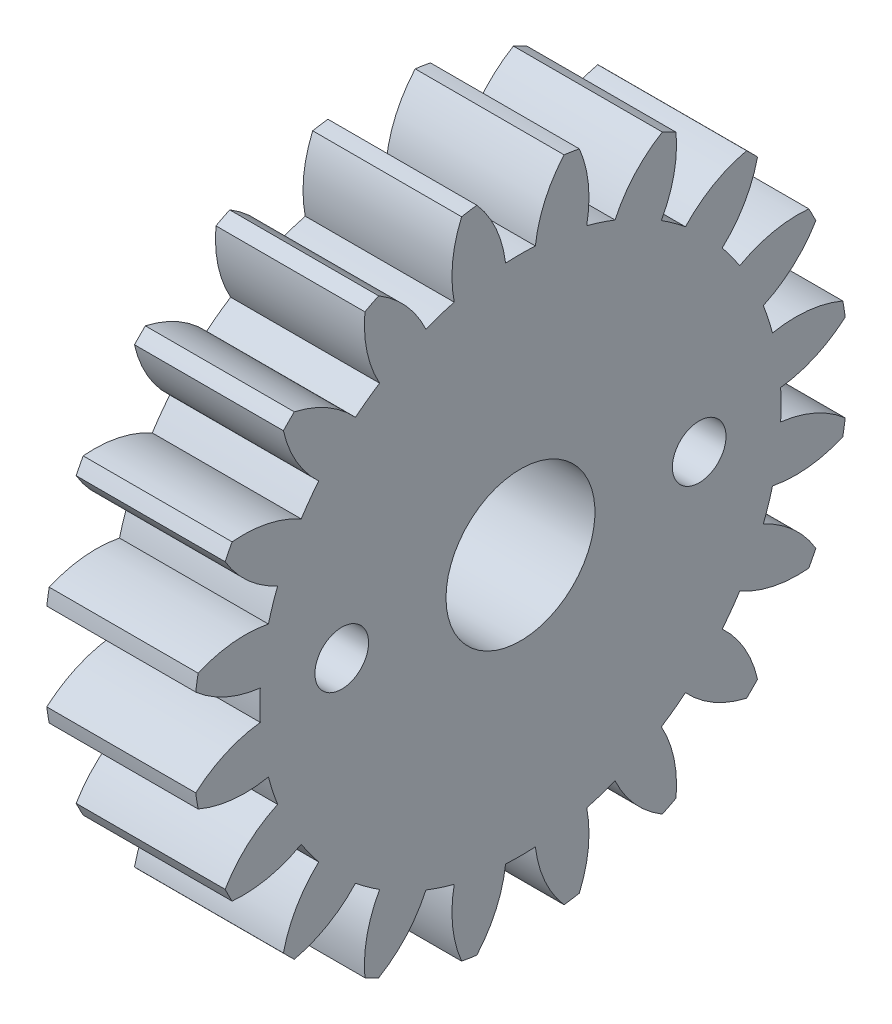
SolidWorks part; units mm, degrees
ref_plane "Plane1" through (0, 0, 0) normal (0, 0, 1) x (1, 0, 0)
ref_plane "Plane2" through (0, 0, 0) normal (0, 1, 0) x (1, 0, 0)
ref_plane "Plane3" through (0, 0, 0) normal (1, 0, 0) x (0, 0, -1)
sketch "HoldingSke" plane through (0, 0, 0) normal (0, 1, 0) x (1, 0, 0)
  line L0 (0, 0) -> (0.9397, -0.342)
  line L1 (-15, 0) -> (100, 0) construction
  line L2 (0, 0) -> (-2.1039, 2.3779)
  line L3 (0, 0) -> (-11.863, 4.5341)
  line L4 (0, 0) -> (8.1152, 2.9537)
  line L5 (0, 0) -> (-46.8476, -17.4728)
  line L6 (0, 0) -> (-4.1448, -2.7965)
  line L7 (-2.1039, 2.3779) -> (8.6586, 51.2059)
  line L8 (-76.2, 54.61) -> (-75.3, 54.61)
  line L9 (-71.009, 38.7566) -> (-53.1078, 45.2721)
  line L10 (-76.2, 71.12) -> (104.1128, 71.12)
  line L11 (0, 0) -> (-5, 0)
  line L12 (-76.2, 101.6) -> (-76.162, 101.6)
  line L13 (24.9733, 27.94) -> (52.9518, 28.4284)
  line L14 (24.9733, 27.94) -> (24.9743, 27.94)
  line L15 (24.9733, 27.94) -> (100.4006, 29.5858)
  line L16 (-63.627, -1) -> (-12.827, -1)
  circle A0 centre (0, 0) radius 2.5
  circle A1 centre (0, 0) radius 8.749
  circle A2 centre (0, 0) radius 37.5
  circle A3 centre (0, 0) radius 2.5
  dimension "MHD" = 17.498
  dimension "Hub_dia" = 75
  dimension "Bore" = 5
  dimension "MBD" = 5
  dimension "Num_teeth" = 20
  dimension "Pitch" = 1
  dimension "Overall_len" = 50
  dimension "Show_teeth" = 20
  dimension "Thickness" = 5
  dimension "OAL" = 50.0001
  dimension "T_dim" = 0.9
  dimension "Ap" = 20
  dimension "H" = 19.05
  dimension "Pitch_radius" = 180.3128
  dimension "Width" = 5
  dimension "Backlash" = 0.038
  dimension "Addendum_fac" = 1
  dimension "Dedendum_fac" = 1.25
  dimension "Clearance_fac" = 0.25
  dimension "Dedendum_add" = 0.001
  dimension "Module" = 1
sketch "BasProSke" plane through (0, 0, 0) normal (0, 1, 0) x (1, 0, 0)
  line L0 (-10, 0) -> (60, 0) construction
  line L1 (0, 0) -> (0, 11)
  line L2 (0, 0) -> (5, 0)
  line L3 (5, 0) -> (5, 11)
  line L4 (5, 11) -> (0, 11)
  dimension "Thickness" = 5
  dimension "Diameter" = 22
revolve "Base-Revolve" add sketch "BasProSke" angle 360 about L0
sketch "TooCutSke" plane through (0, 0, 0) normal (1, 0, 0) x (0, 0, -1)
  line L1 (0, 0) -> (0, 107) construction
  line L2 (0, 0) -> (-0.8511, 9.9637) construction
  line L3 (0, 0) -> (-3.1206, 19.7028) construction
  line L4 (-0.8511, 9.9637) -> (-1.5603, 9.8514) construction
  arc A0 (0.4999, 8.7347) -> (-0.4999, 8.7347) centre (0, 0) ccw
  arc A1 (1.4852, 10.9249) -> (-1.4852, 10.9249) centre (0, 0) ccw
  circle A2 centre (0, 0) radius 10 construction
  circle A3 centre (0, 0) radius 9.3969 construction
  arc A4 (-0.4999, 8.7347) -> (-1.4852, 10.9249) centre (-4.4722, 8.2645) ccw
  arc A5 (1.4852, 10.9249) -> (0.4999, 8.7347) centre (4.4722, 8.2645) ccw
  dimension "Root_dia" = 17.498
  dimension "Overcut_dia" = 22.0508
  dimension "Pitch_dia" = 20
  dimension "Base_dia" = 18.7939
  dimension "Flank_rad" = 4
  dimension "Half_ang" = 9
  dimension "Half_CT" = 0.7181
extrude "ToothCut" cut sketch "TooCutSke" along normal through all
fillet "Breaks" [suppressed] radius 0.02
fillet "RootFillets" [suppressed] radius 0.251
pattern_circular "TeethCuts" count 20 every 18 about axis through (-10, 0, 0) along (1, 0, 0) of "ToothCut", "RootFillets", "Breaks"
sketch "HubNeaOneSke" plane through (0, 0, 0) normal (-1, 0, 0) x (0, 0, 1)
  circle A0 centre (0, 0) radius 8.749
  dimension "Diameter" = 17.498
extrude "HubNearOne" [suppressed] add sketch "HubNeaOneSke" along normal blind 45.0001
sketch "HubNeaBotSke" plane through (0, 0, 0) normal (-1, 0, 0) x (0, 0, 1)
  circle A0 centre (0, 0) radius 8.749
  dimension "Diameter" = 17.498
extrude "HubNearBoth" [suppressed] add sketch "HubNeaBotSke" along normal blind 22.5
ref_plane "FarPln" through (5, 0, 0) normal (1, 0, 0) x (0, 0, -1)
sketch "HubFarSke" plane through (5, 0, 0) normal (1, 0, 0) x (0, 0, -1)
  circle A0 centre (0, 0) radius 8.749
  dimension "Diameter" = 17.498
extrude "HubFar" [suppressed] add sketch "HubFarSke" along normal blind 22.5
sketch "BorSke" plane through (0, 0, 0) normal (1, 0, 0) x (0, 0, -1)
  circle A0 centre (0, 0) radius 2.5
  dimension "Diameter" = 5
extrude "Bore" cut sketch "BorSke" along normal mid plane 100.0001
sketch "KeySke" plane through (0, 0, 0) normal (1, 0, 0) x (0, 0, -1)
  line L0 (-1, 0) -> (-1, 3.4)
  line L1 (-1, 3.4) -> (1, 3.4)
  line L2 (1, 3.4) -> (1, 0)
  line L3 (0, 0) -> (0, 34) construction
  line L4 (-1, 0) -> (1, 0)
  dimension "Offset" = 3.4
  dimension "Width" = 2
extrude "Keyway" [suppressed] cut sketch "KeySke" along normal mid plane 100.0001
pattern_circular "Keyway2" [suppressed] count 2 every 90 about axis through (-10, 0, 0) along (1, 0, 0)
sketch "Sketch1" plane through (5, 0, 0) normal (1, 0, 0) x (0, 0, -1)
  line L0 (0, 0) -> (6, 0) construction
  line L1 (0, 0) -> (0, 5.6094) construction
  circle A0 centre (6, 0) radius 0.9
  circle A1 centre (-6, 0) radius 0.9
  dimension "D2" = 1.8
  dimension "D1" = 6
extrude "Cut-Extrude1" cut sketch "Sketch1" against normal blind 10
equation "' \"Module@HoldingSke\" = 6.35"
equation "' \"Num_teeth@HoldingSke\" = 12"
equation "' \"Ap@HoldingSke\" =  20"
equation "' \"Ap@HoldingSke\" = 20"
equation "' \"Width@HoldingSke\" = 0.5 * 25.4"
equation "' \"Hub_dia@HoldingSke\"= 1 * 25.4"
equation "' \"Hub_dia@HoldingSke\" = 1 * 25.4"
equation "' \"Overall_len@HoldingSke\" = 1.0 * 25.4"
equation "' \"Bore@HoldingSke\" = 0.75 * 25.4"
equation "' \"T_dim@HoldingSke\" = 0.1 * 25.4"
equation "' \"Width@KeySke\" = 0.25 * 25.4"
equation "' \"Show_teeth@HoldingSke\" = 13"
equation "' \"Backlash@HoldingSke\" = 0.009 * 25.4"
equation "' \"Addendum_fac@HoldingSke\" = 1.0"
equation "' \"Dedendum_fac@HoldingSke\" = 1.25"
equation "' \"Dedendum_add@HoldingSke\" = 0.00005 * 25.4"
equation "' \"Clearance_fac@HoldingSke\" = 0.25"
equation "\"Pitch@HoldingSke\" = 1 / \"Module@HoldingSke\""
equation "\"Overcut_dia@TooCutSke\" = (\"Num_teeth@HoldingSke\" + 2 * \"Addendum_fac@HoldingSke\") / \"Pitch@HoldingSke\" + 0.002 * 25.4"
equation "\"Pitch_dia@TooCutSke\" = \"Num_teeth@HoldingSke\" / \"Pitch@HoldingSke\""
equation "\"Base_dia@TooCutSke\" = \"Num_teeth@HoldingSke\" / \"Pitch@HoldingSke\" * cos((\"Ap@HoldingSke\"  * 3.14159265 / 180))"
equation "\"Root_dia@TooCutSke\" = (\"Num_teeth@HoldingSke\" + 2) / \"Pitch@HoldingSke\" - 2 * (\"Addendum_fac@HoldingSke\" + \"Dedendum_fac@HoldingSke\") / \"Pitch@HoldingSke\" - \"Dedendum_add@HoldingSke\" * 2"
equation "\"Half_ang@TooCutSke\" = 180 / \"Num_teeth@HoldingSke\""
equation "\"Half_CT@TooCutSke\" = \"Num_teeth@HoldingSke\" / \"Pitch@HoldingSke\" * sin((3.14159265 / 2 / \"Num_teeth@HoldingSke\")) / 2 - 7 * \"Backlash@HoldingSke\" / 4"
equation "\"Flank_rad@TooCutSke\" = \"Num_teeth@HoldingSke\" / \"Pitch@HoldingSke\" / 5"
equation "\"Radius@RootFillets\" = \"Clearance_fac@HoldingSke\" / \"Pitch@HoldingSke\" + \"Dedendum_add@HoldingSke\""
equation "\"Break_rad@Breaks\" = 0.02 / \"Pitch@HoldingSke\""
equation "\"Thickness@HoldingSke\" = \"Width@HoldingSke\""
equation "\"OAL@HoldingSke\" = \"Thickness@HoldingSke\""
equation "\"MHD@HoldingSke\" = (\"Num_teeth@HoldingSke\" + 2) / \"Pitch@HoldingSke\" - 2 * (\"Addendum_fac@HoldingSke\" + \"Dedendum_fac@HoldingSke\")  / \"Pitch@HoldingSke\" - \"Dedendum_add@HoldingSke\" * 2"
equation "\"MBD@HoldingSke\" = (\"Num_teeth@HoldingSke\" + 2) / \"Pitch@HoldingSke\" - 2 * (\"Addendum_fac@HoldingSke\" + \"Dedendum_fac@HoldingSke\")  / \"Pitch@HoldingSke\" - \"Dedendum_add@HoldingSke\" * 2 - 0.002 * 25.4"
equation "\"MHD@HoldingSke\" = ((sgn( \"MHD@HoldingSke\" - \"Hub_dia@HoldingSke\" )-1)*( \"MHD@HoldingSke\" - \"Hub_dia@HoldingSke\" ))/-2+ \"Hub_dia@HoldingSke\""
equation "\"MBD@HoldingSke\" = ((sgn( \"MBD@HoldingSke\" - \"Bore@HoldingSke\" )-1)*( \"MBD@HoldingSke\" - \"Bore@HoldingSke\" ))/-2+ \"Bore@HoldingSke\""
equation "\"OAL@HoldingSke\" = ((sgn( \"OAL@HoldingSke\" - \"Overall_len@HoldingSke\" )+1)*( \"OAL@HoldingSke\" - \"Overall_len@HoldingSke\" ))/2 + \"Overall_len@HoldingSke\" + 0.000002 * 25.4"
equation "\"Num_teeth@TeethCuts\" = int( \"Show_teeth@HoldingSke\" ) + 1"
equation "\"Num_teeth@TeethCuts\" = ((sgn( \"Num_teeth@TeethCuts\" - \"Num_teeth@HoldingSke\" )-1)*( \"Num_teeth@TeethCuts\" - \"Num_teeth@HoldingSke\" ))/-2+ \"Num_teeth@HoldingSke\""
equation "\"Num_teeth@TeethCuts\" = ((sgn( \"Num_teeth@TeethCuts\" - 2.0)+1)*( \"Num_teeth@TeethCuts\" - 2.0))/2 +2.0"
equation "\"Angle@TeethCuts\" = 360.0 / \"Num_teeth@HoldingSke\""
equation "\"Diameter@BasProSke\" = (\"Num_teeth@HoldingSke\" + 2 * \"Addendum_fac@HoldingSke\") / \"Pitch@HoldingSke\""
equation "\"Thickness@BasProSke\"  = \"Thickness@HoldingSke\""
equation "' \"Fillet_rad@BasProSke\" =  \"Thickness@HoldingSke\" * 0.05"
equation "' \"Fillet_rad@BasProSke\" = \"Thickness@HoldingSke\" * 0.05"
equation "\"MHD@HoldingSke\" = ((sgn( \"MHD@HoldingSke\" - \"Root_dia@TooCutSke\" )-1)*( \"MHD@HoldingSke\" - \"Root_dia@TooCutSke\" ))/-2+ \"Root_dia@TooCutSke\""
equation "\"Diameter@HubNeaOneSke\" = \"MHD@HoldingSke\""
equation "\"Length@HubNearOne\" = \"OAL@HoldingSke\" - \"Thickness@BasProSke\""
equation "\"Diameter@HubNeaBotSke\" = \"MHD@HoldingSke\""
equation "\"Length@HubNearBoth\" = ( \"OAL@HoldingSke\" - \"Thickness@BasProSke\" ) / 2.0"
equation "\"Thickness@FarPln\" = \"Thickness@BasProSke\""
equation "\"Diameter@HubFarSke\" = \"MHD@HoldingSke\""
equation "\"Length@HubFar\" = ( \"OAL@HoldingSke\" - \"Thickness@BasProSke\" ) / 2.0"
equation "\"Diameter@BorSke\" = \"MBD@HoldingSke\""
equation "\"D1@Bore\" = \"OAL@HoldingSke\" * 2.0"
equation "\"D1@Keyway\" = \"OAL@HoldingSke\" * 2.0"
equation "\"Offset@KeySke\" = \"T_dim@HoldingSke\" + \"MBD@HoldingSke\" / 2.0"
